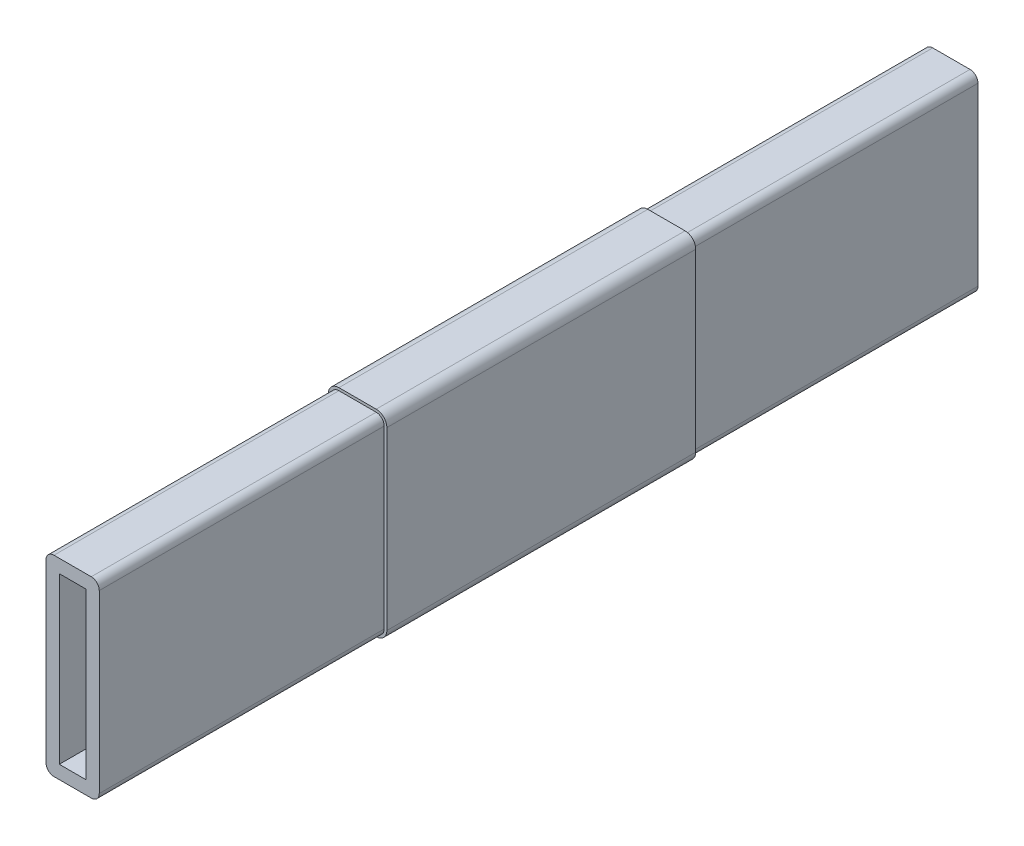
SolidWorks part; units mm, degrees
material "1.0037 (S235JR)"
ref_plane "Front Plane" through (0, 0, 0) normal (0, 0, 1) x (1, 0, 0)
ref_plane "Top Plane" through (0, 0, 0) normal (0, 1, 0) x (1, 0, 0)
ref_plane "Right Plane" through (0, 0, 0) normal (1, 0, 0) x (0, 0, -1)
sketch "Sketch1" plane through (0, 0, 0) normal (0, 0, 1) x (1, 0, 0)
  line L6 (-11, -37) -> (11, -37)
  line L7 (-11, -37) -> (-11, 37)
  line L8 (-11, 37) -> (11, 37)
  line L9 (11, -37) -> (11, 37)
  line L10 (-11, -37) -> (11, 37) construction
  line L11 (-11, 37) -> (11, -37) construction
  point P0 (0, 0)
  dimension "D1" = 22
  dimension "D2" = 74
extrude "Boss-Extrude1" add sketch "Sketch1" along normal blind 330
sketch "Sketch4" plane through (0, 0, 330) normal (0, 0, 1) x (1, 0, 0)
  line L0 (11, -37) -> (11, 37) construction
  line L1 (-5, -31) -> (5, -31)
  line L2 (-5, -31) -> (-5, 31)
  line L3 (-5, 31) -> (5, 31)
  line L4 (5, -31) -> (5, 31)
  line L5 (-5, -31) -> (5, 31) construction
  line L6 (-5, 31) -> (5, -31) construction
  line L7 (-11, -37) -> (11, -37) construction
  point P0 (0, 0)
  dimension "D1" = 6
  dimension "D2" = 6
extrude "Cut-Extrude2" cut sketch "Sketch4" against normal through all both and the other way through all
sketch "Sketch6" plane through (0, 0, 330) normal (0, 0, 1) x (1, 0, 0)
  line L0 (11, 37) -> (-11, 37) construction
  line L1 (-10, -36) -> (10, -36)
  line L2 (-10, -36) -> (-10, 36)
  line L3 (-10, 36) -> (10, 36)
  line L4 (10, -36) -> (10, 36)
  line L5 (-10, -36) -> (10, 36) construction
  line L6 (-10, 36) -> (10, -36) construction
  line L7 (11, -37) -> (11, 37) construction
  line L9 (-11, -37) -> (11, -37)
  line L10 (-11, -37) -> (-11, 37)
  line L11 (-11, 37) -> (11, 37)
  line L12 (11, -37) -> (11, 37)
  line L13 (-11, -37) -> (11, 37) construction
  line L14 (-11, 37) -> (11, -37) construction
  point P0 (0, 0)
  point P10 (0, 0)
  dimension "D1" = 1
  dimension "D2" = 1
extrude "Cut-Extrude4" cut sketch "Sketch6" against normal blind 107
sketch "Sketch7" plane through (0, 0, 0) normal (0, 0, -1) x (-1, 0, 0)
  line L5 (-11, 37) -> (11, 37) construction
  line L6 (-10, -36) -> (10, -36)
  line L11 (-10, -36) -> (-10, 36)
  line L12 (-10, 36) -> (10, 36)
  line L13 (10, -36) -> (10, 36)
  line L14 (-10, -36) -> (10, 36) construction
  line L15 (-10, 36) -> (10, -36) construction
  line L17 (11, 37) -> (11, -37) construction
  line L19 (-11, -37) -> (11, -37)
  line L20 (-11, -37) -> (-11, 37)
  line L21 (-11, 37) -> (11, 37)
  line L22 (11, -37) -> (11, 37)
  line L23 (-11, -37) -> (11, 37) construction
  line L24 (-11, 37) -> (11, -37) construction
  point P0 (0, 0)
  point P10 (0, 0)
  dimension "D1" = 1
  dimension "D2" = 1
extrude "Cut-Extrude5" cut sketch "Sketch7" against normal blind 107
sketch "Sketch9" plane through (0, 0, 330) normal (0, 0, 1) x (1, 0, 0)
  line L0 (10, 36) -> (-10, 36) construction
  line L1 (-5, -31) -> (5, -31)
  line L2 (-5, -31) -> (-5, 31)
  line L3 (-5, 31) -> (5, 31)
  line L4 (5, -31) -> (5, 31)
  line L5 (-5, -31) -> (5, 31) construction
  line L6 (-5, 31) -> (5, -31) construction
  line L7 (10, -36) -> (10, 36) construction
  point P0 (0, 0)
  dimension "D1" = 5
  dimension "D2" = 5
fillet "Fillet1" radius 3 8 edges at (10, -36, 276.5) (-10, -36, 276.5) (10, 36, 276.5) (-10, 36, 276.5) (10, 36, 53.5) (10, -36, 53.5) (-10, -36, 53.5) (-10, 36, 53.5)
fillet "Fillet2" radius 4 4 edges at (11, 37, 165) (-11, 37, 165) (-11, -37, 165) (11, -37, 165)
